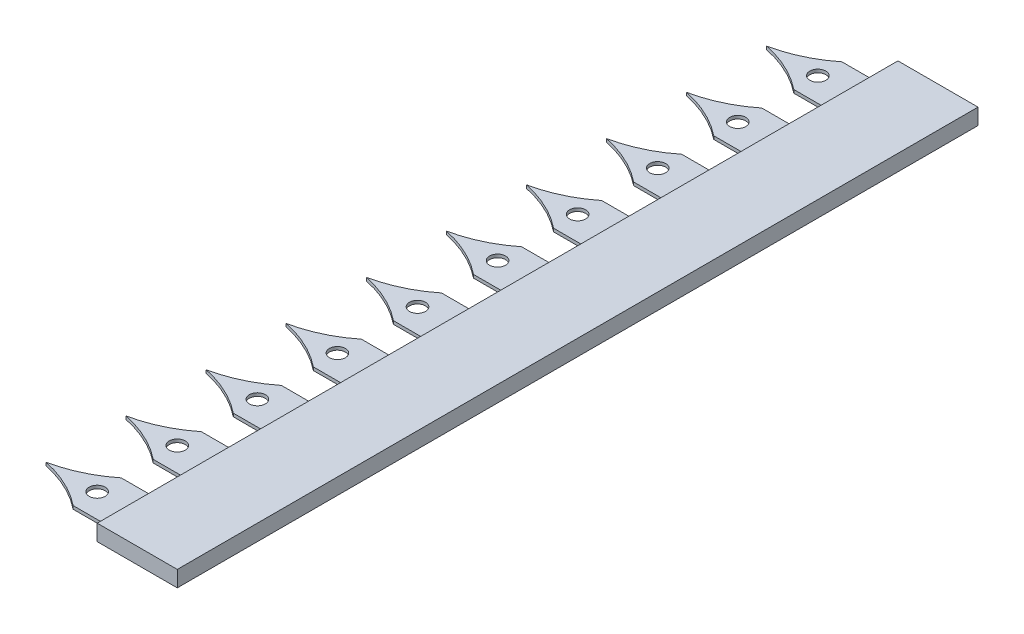
SolidWorks part; units mm, degrees
material "Stainless Steel (ferritic)"
ref_plane "Front Plane" through (0, 0, 0) normal (0, 0, 1) x (1, 0, 0)
ref_plane "Top Plane" through (0, 0, 0) normal (0, 1, 0) x (1, 0, 0)
ref_plane "Right Plane" through (0, 0, 0) normal (1, 0, 0) x (0, 0, -1)
sketch "Sketch1" plane through (0, 0, 0) normal (0, 0, 1) x (1, 0, 0)
  line L1 (-25, -5) -> (25, -5)
  line L2 (-25, -5) -> (-25, 5)
  line L3 (-25, 5) -> (25, 5)
  line L4 (25, -5) -> (25, 5)
  line L5 (-25, -5) -> (25, 5) construction
  line L6 (-25, 5) -> (25, -5) construction
  point P0 (0, 0)
  dimension "D1" = 50
  dimension "D2" = 10
extrude "Boss-Extrude1" add sketch "Sketch1" along normal blind 50
sketch "Sketch2" plane through (0, -5, 0) normal (0, -1, 0) x (1, 0, 0)
  line L0 (-25, 50) -> (25, 50) construction
  line L1 (-25, 10) -> (-50, 10)
  line L2 (-25, 10) -> (-25, 40)
  line L3 (-25, 40) -> (-50, 40)
  line L4 (-50, 10) -> (-50, 40)
  line L5 (-25, 10) -> (-50, 40) construction
  line L6 (-25, 40) -> (-50, 10) construction
  line L8 (-50, 25) -> (-37.5, 25) construction
  circle A0 centre (-50, 25) radius 5
  spline S0 degree 2 poles (-50, 10) (-64.1272, 21.24) (-81.9691, 25) knots 0 0 0 1 1 1
  spline S1 degree 2 poles (-50, 40) (-64.1272, 28.76) (-81.9691, 25) knots 0 0 0 1 1 1
  point P0 (-37.5, 25)
  dimension "D5" = 10
  dimension "D1" = 30
  dimension "D2" = 10
  dimension "D3" = 0
  dimension "D4" = 25
extrude "Boss-Extrude2" add sketch "Sketch2" against normal blind 2
pattern_linear "LPattern1" count 10 spacing 50 along (0, 0, -1) of "Boss-Extrude2", "Boss-Extrude1"
